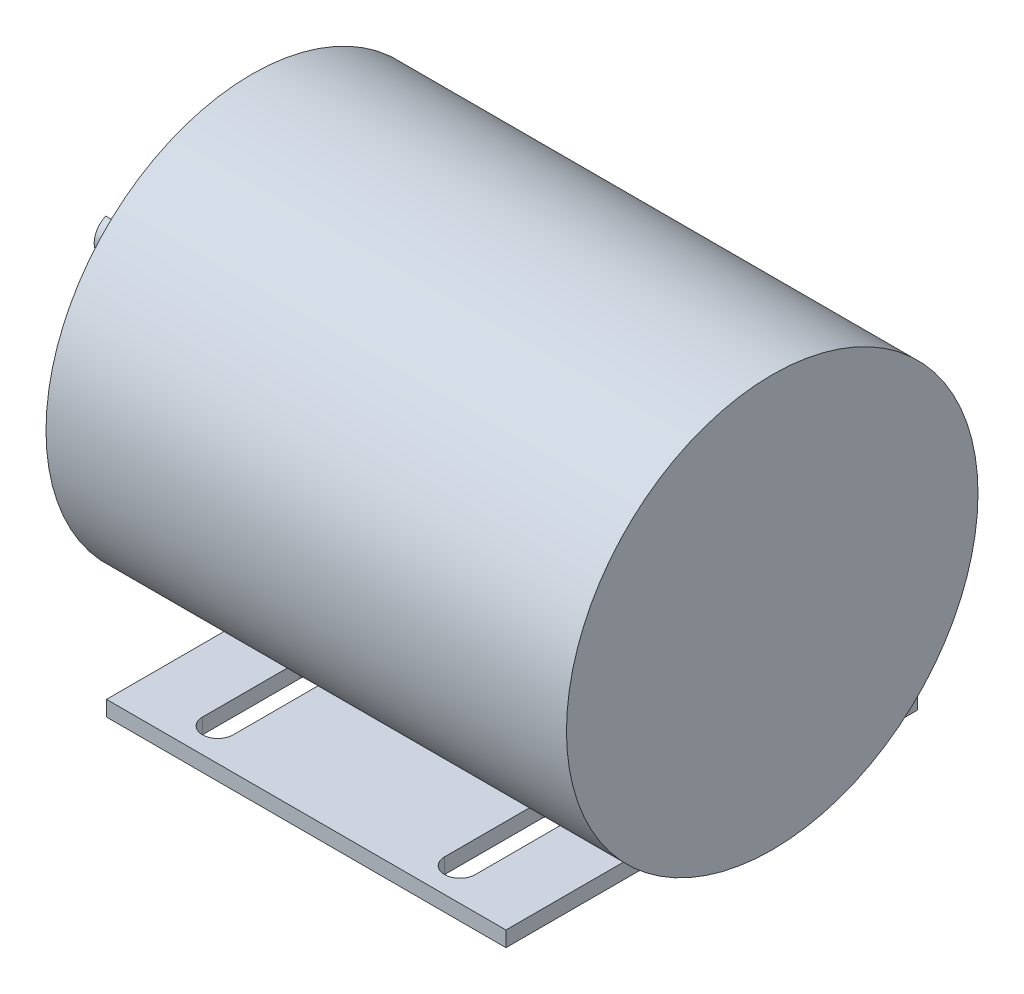
SolidWorks part; units mm, degrees
ref_plane "Alzado" through (0, 0, 0) normal (0, 0, 1) x (1, 0, 0)
ref_plane "Planta" through (0, 0, 0) normal (0, 1, 0) x (1, 0, 0)
ref_plane "Vista lateral" through (0, 0, 0) normal (1, 0, 0) x (0, 0, -1)
sketch "Croquis1" plane through (0, 0, 0) normal (1, 0, 0) x (0, 0, -1)
  circle A0 centre (0, 0) radius 85
  dimension "D1" = 170
extrude "Saliente-Extruir1" add sketch "Croquis1" along normal blind 215
sketch "Croquis2" plane through (0, 0, 0) normal (-1, 0, 0) x (0, 0, 1)
  circle A0 centre (0, 0) radius 7.9375
  dimension "D1" = 15.875
extrude "Saliente-Extruir2" add sketch "Croquis2" along normal blind 57.15
ref_plane "Plano1" through (0, -90, 0) normal (0, 1, 0) x (1, 0, 0)
sketch "Croquis4" plane through (0, -90, 0) normal (0, 1, 0) x (1, 0, 0)
  line L0 (215, 85) -> (0, 85) construction
  line L1 (25, 85) -> (190, 85)
  line L2 (25, 85) -> (25, -85)
  line L3 (25, -85) -> (190, -85)
  line L4 (190, 85) -> (190, -85)
  line L5 (0, -85) -> (215, -85) construction
  line L6 (0, 85) -> (0, -85) construction
  line L7 (215, -85) -> (215, 85) construction
  line L8 (25, 85) -> (190, -85) construction
  line L9 (190, 85) -> (25, -85) construction
  dimension "D1" = 25
  dimension "D2" = 25
extrude "Saliente-Extruir3" add sketch "Croquis4" along normal blind 6.35
sketch "Croquis5" plane through (-57.15, 0, 0) normal (-1, 0, 0) x (0, 0, 1)
  line L0 (0, 0) -> (0, 9.525) construction
  line L1 (-3.175, 7.9375) -> (3.175, 7.9375) construction
  line L2 (-3.175, 4.7625) -> (3.175, 4.7625)
  line L3 (-3.175, 4.7625) -> (-3.175, 11.1125)
  line L4 (-3.175, 11.1125) -> (3.175, 11.1125)
  line L5 (3.175, 4.7625) -> (3.175, 11.1125)
  circle A0 centre (0, 0) radius 7.9375
  circle A1 centre (0, 0) radius 7.9375 construction
  point P10 (0, 4.7625)
  circle M8 centre (0, 0) radius 7.9375
  dimension "D1" = 6.35
extrude "Cortar-Extruir1" cut sketch "Croquis5" against normal blind 25 contours L2 L5 L3 M8
sketch "Croquis6" plane through (0, -90, 0) normal (0, -1, 0) x (1, 0, 0)
sketch "Croquis7" plane through (0, -90, 0) normal (0, -1, 0) x (1, 0, 0)
  line L0 (51.15, 71.5152) -> (51.15, 31.5152)
  line L1 (63.85, 31.5152) -> (63.85, 71.5152)
  line L2 (25, 85) -> (190, -85) construction
  line L3 (190, 85) -> (25, -85) construction
  line L5 (57.5, 31.5152) -> (57.5, 71.5152) construction
  line L6 (151.15, 71.5152) -> (151.15, 31.5152)
  line L7 (163.85, 31.5152) -> (163.85, 71.5152)
  line L8 (51.15, -31.5152) -> (51.15, -71.5152)
  line L9 (63.85, -71.5152) -> (63.85, -31.5152)
  line L10 (151.15, -31.5152) -> (151.15, -71.5152)
  line L11 (163.85, -71.5152) -> (163.85, -31.5152)
  line L13 (157.5, 71.5152) -> (157.5, 31.5152) construction
  line L14 (157.5, -71.5152) -> (157.5, -31.5152) construction
  line L15 (57.5, -71.5152) -> (57.5, -31.5152) construction
  arc A0 (51.15, 31.5152) -> (63.85, 31.5152) centre (57.5, 31.5152) ccw
  arc A1 (63.85, 71.5152) -> (51.15, 71.5152) centre (57.5, 71.5152) ccw
  arc A2 (151.15, 31.5152) -> (163.85, 31.5152) centre (157.5, 31.5152) ccw
  arc A3 (163.85, 71.5152) -> (151.15, 71.5152) centre (157.5, 71.5152) ccw
  arc A4 (51.15, -71.5152) -> (63.85, -71.5152) centre (57.5, -71.5152) ccw
  arc A5 (63.85, -31.5152) -> (51.15, -31.5152) centre (57.5, -31.5152) ccw
  arc A6 (151.15, -71.5152) -> (163.85, -71.5152) centre (157.5, -71.5152) ccw
  arc A7 (163.85, -31.5152) -> (151.15, -31.5152) centre (157.5, -31.5152) ccw
  point P15 (57.5, 51.5152)
  point P36 (157.5, 51.5152)
  point P37 (157.5, -51.5152)
  point P38 (57.5, -51.5152)
  dimension "D1" = 12.7
  dimension "D2" = 40
  dimension "D3" = 100
extrude "Cortar-Extruir2" cut sketch "Croquis7" against normal blind 10 contours A1 L0 A0 L1 | A3 L6 A2 L7 | A5 L8 A4 L9 | A7 L10 A6 L11
